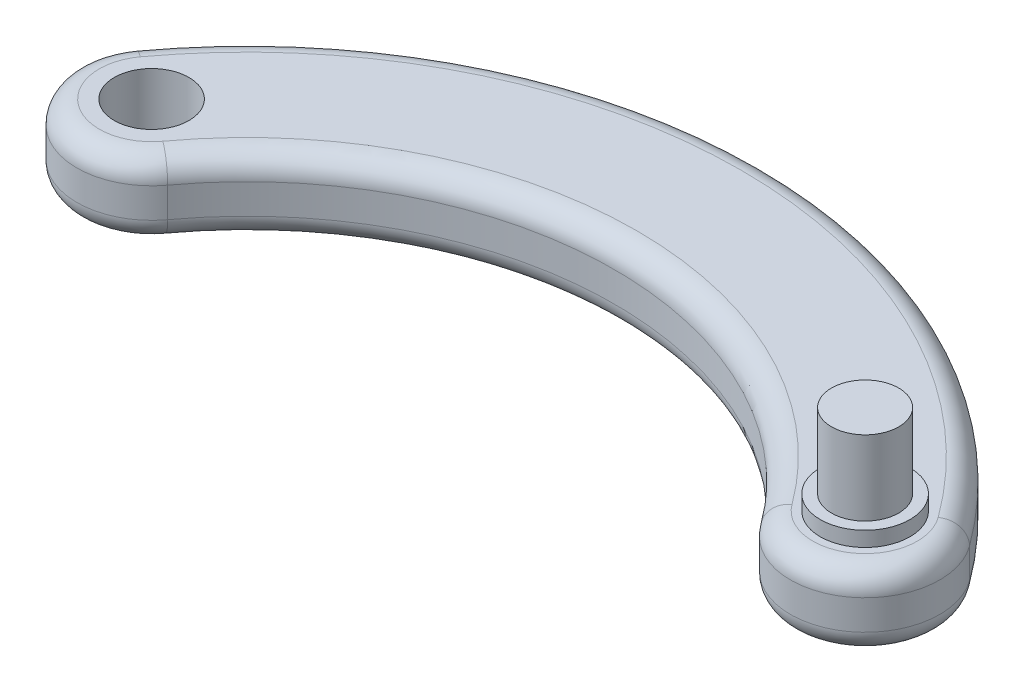
SolidWorks part; units mm, degrees
ref_plane "Front Plane" through (0, 0, 0) normal (0, 0, 1) x (1, 0, 0)
ref_plane "Top Plane" through (0, 0, 0) normal (0, 1, 0) x (1, 0, 0)
ref_plane "Right Plane" through (0, 0, 0) normal (1, 0, 0) x (0, 0, -1)
sketch "Sketch2" plane through (0, 0, 0) normal (0, 1, 0) x (1, 0, 0)
  line L1 (-47.75, -84.2036) -> (-47.75, -91.3748)
  circle A0 centre (-95.5, 0) radius 5
  circle A1 centre (0, 0) radius 5
  arc A3 (-103.5654, 5.9118) -> (-87.4346, -5.9118) centre (-95.5, 0) ccw
  arc A4 (-8.0654, -5.9118) -> (8.0654, 5.9118) centre (0, 0) ccw
  arc A6 (-8.0654, -5.9118) -> (-87.4346, -5.9118) centre (-47.75, -35) ccw
  arc A7 (8.0654, 5.9118) -> (-103.5654, 5.9118) centre (-47.75, -35) ccw
extrude "Boss-Extrude1" add sketch "Sketch2" along normal blind 10 contours A4 A7 A3 A6 A0 A1
fillet "Fillet1" radius 3 8 edges at (5.9118, 0, 8.0654) (-47.75, 0, -14.2036) (-101.4118, 0, 8.0654) (5.9118, 10, 8.0654) (-47.75, 10, -14.2036) (-101.4118, 10, 8.0654) (-47.75, 0, -34.2036) (-47.75, 10, -34.2036)
sketch "Sketch3" plane through (0, 10, 0) normal (0, 1, 0) x (1, 0, 0)
  circle A0 centre (0, 0) radius 5
extrude "Boss-Extrude2" add sketch "Sketch3" against normal up to surface (10 mm away) up to face at (-47.75, 0, -9.2789)
sketch "Sketch4" plane through (0, 10, 0) normal (0, 1, 0) x (1, 0, 0)
  circle A0 centre (0, 0) radius 4.5
  circle A1 centre (0, 0) radius 6
extrude "Boss-Extrude3" add sketch "Sketch4" along normal blind 2
sketch "Sketch6" plane through (0, 10, 0) normal (0, 1, 0) x (1, 0, 0)
  circle A0 centre (0, 0) radius 4.5
extrude "Boss-Extrude4" add sketch "Sketch6" along normal blind 12
